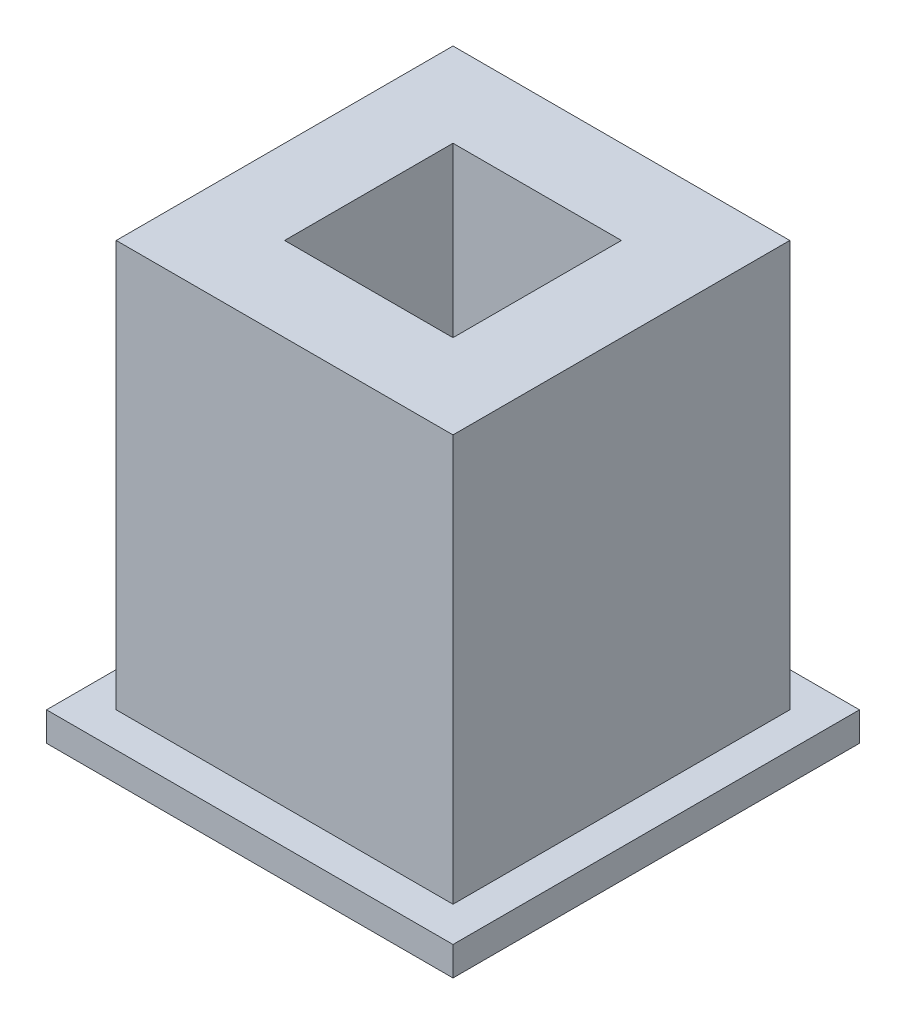
SolidWorks part; units mm, degrees
ref_plane "Front Plane" through (0, 0, 0) normal (0, 0, 1) x (1, 0, 0)
ref_plane "Top Plane" through (0, 0, 0) normal (0, 1, 0) x (1, 0, 0)
ref_plane "Right Plane" through (0, 0, 0) normal (1, 0, 0) x (0, 0, -1)
sketch "Sketch1" plane through (0, 0, 0) normal (0, 1, 0) x (1, 0, 0)
  line L1 (0, 0) -> (5.8, 0)
  line L2 (0, 0) -> (0, 5.8)
  line L3 (0, 5.8) -> (5.8, 5.8)
  line L4 (5.8, 0) -> (5.8, 5.8)
  dimension "D1" = 5.8
extrude "Boss-Extrude1" add sketch "Sketch1" along normal blind 7
sketch "Sketch3" plane through (0, 7, 0) normal (0, 1, 0) x (1, 0, 0)
  line L0 (2.9, 4.35) -> (2.9, 5.8) construction
  line L1 (1.45, 4.35) -> (4.35, 4.35)
  line L2 (1.45, 4.35) -> (1.45, 1.45)
  line L3 (1.45, 1.45) -> (4.35, 1.45)
  line L4 (4.35, 4.35) -> (4.35, 1.45)
  line L5 (5.8, 5.8) -> (0, 5.8) construction
  line L6 (4.35, 2.9) -> (5.8, 2.9) construction
  line L7 (5.8, 0) -> (5.8, 5.8) construction
  dimension "D1" = 2.9
extrude "Cut-Extrude1" cut sketch "Sketch3" against normal blind 3.8
sketch "Sketch4" plane through (0, 0, 0) normal (0, -1, 0) x (1, 0, 0)
  line L0 (2.9, 0) -> (2.9, 0.6) construction
  line L1 (-0.6, 0.6) -> (6.4, 0.6)
  line L2 (-0.6, 0.6) -> (-0.6, -6.4)
  line L3 (-0.6, -6.4) -> (6.4, -6.4)
  line L4 (6.4, 0.6) -> (6.4, -6.4)
  line L5 (0, 0) -> (5.8, 0) construction
  line L6 (5.8, -2.9) -> (6.4, -2.9) construction
  line L7 (5.8, 0) -> (5.8, -5.8) construction
  dimension "D2" = 7
extrude "Boss-Extrude2" add sketch "Sketch4" along normal blind 1.7
chamfer "Chamfer1" distance 1.2 angle 45 4 edges at (-0.6, -1.7, -2.9) (2.9, -1.7, 0.6) (6.4, -1.7, -2.9) (2.9, -1.7, -6.4)
